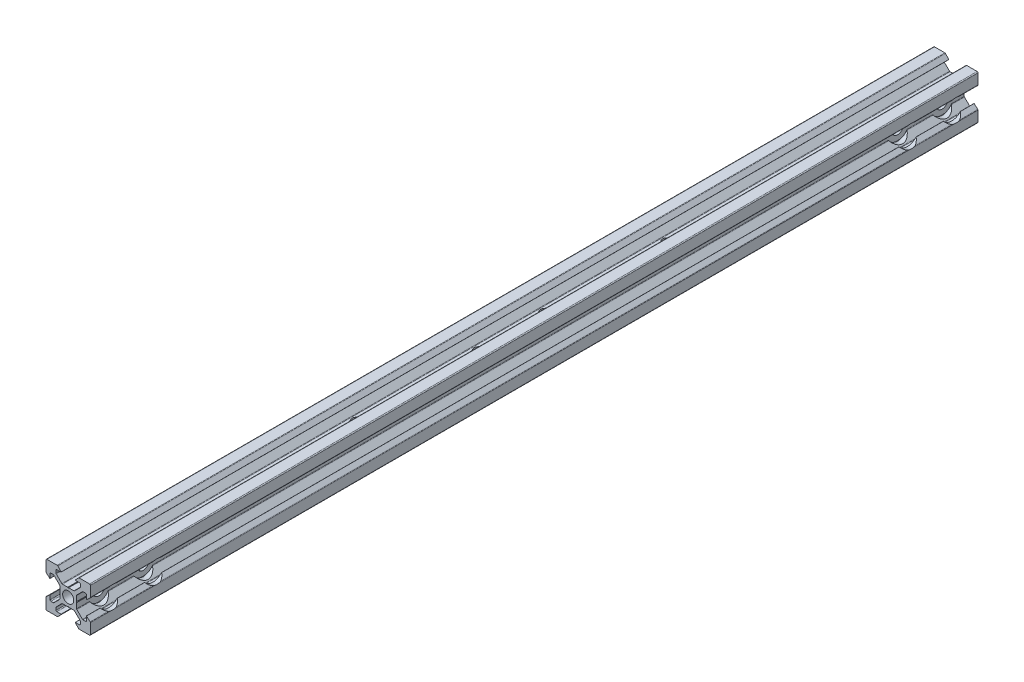
SolidWorks part; units mm, degrees
material "6063-T5"
ref_plane "前视基准面" through (0, 0, 0) normal (0, 0, 1) x (1, 0, 0)
ref_plane "上视基准面" through (0, 0, 0) normal (0, 1, 0) x (1, 0, 0)
ref_plane "右视基准面" through (0, 0, 0) normal (1, 0, 0) x (0, 0, -1)
sketch "草图1" plane through (0, 0, 0) normal (0, 0, 1) x (1, 0, 0)
  line L0 (0, 0) -> (13486.7145, 0) construction
  line L1 (0, 0) -> (0, 13486.7145) construction
  line L2 (0, 0) -> (9536.5473, 9536.5473) construction
  line L3 (0.2, 3.8) -> (2.5737, 3.8)
  line L4 (2.8565, 3.9172) -> (5.3828, 6.4435)
  line L5 (5.5, 6.7263) -> (5.5, 7.8)
  line L6 (5.1, 8.2) -> (3.2, 8.2)
  line L7 (3.1681, 8.2732) -> (4.6563, 9.8725)
  line L8 (4.9492, 10) -> (9.6, 10)
  line L9 (3.8, 0.2) -> (3.8, 2.5737)
  line L10 (3.9172, 2.8565) -> (6.4435, 5.3828)
  line L11 (6.7263, 5.5) -> (7.8, 5.5)
  line L12 (8.2, 5.1) -> (8.2, 3.2)
  line L13 (8.2732, 3.1681) -> (9.8725, 4.6563)
  line L14 (10, 4.9492) -> (10, 9.6)
  line L15 (3.8, -0.2) -> (3.8, -2.5737)
  line L16 (3.9172, -2.8565) -> (6.4435, -5.3828)
  line L17 (6.7263, -5.5) -> (7.8, -5.5)
  line L18 (8.2, -5.1) -> (8.2, -3.2)
  line L19 (8.2732, -3.1681) -> (9.8725, -4.6563)
  line L20 (10, -4.9492) -> (10, -9.6)
  line L21 (4.9492, -10) -> (9.6, -10)
  line L22 (3.1681, -8.2732) -> (4.6563, -9.8725)
  line L23 (5.1, -8.2) -> (3.2, -8.2)
  line L24 (5.5, -6.7263) -> (5.5, -7.8)
  line L25 (2.8565, -3.9172) -> (5.3828, -6.4435)
  line L26 (0.2, -3.8) -> (2.5737, -3.8)
  line L27 (-0.2, -3.8) -> (-2.5737, -3.8)
  line L28 (-2.8565, -3.9172) -> (-5.3828, -6.4435)
  line L29 (-5.5, -6.7263) -> (-5.5, -7.8)
  line L30 (-5.1, -8.2) -> (-3.2, -8.2)
  line L31 (-3.1681, -8.2732) -> (-4.6563, -9.8725)
  line L32 (-4.9492, -10) -> (-9.6, -10)
  line L33 (-10, -4.9492) -> (-10, -9.6)
  line L34 (-8.2732, -3.1681) -> (-9.8725, -4.6563)
  line L35 (-8.2, -5.1) -> (-8.2, -3.2)
  line L36 (-6.7263, -5.5) -> (-7.8, -5.5)
  line L37 (-3.9172, -2.8565) -> (-6.4435, -5.3828)
  line L38 (-3.8, -0.2) -> (-3.8, -2.5737)
  line L39 (-3.8, 0.2) -> (-3.8, 2.5737)
  line L40 (-3.9172, 2.8565) -> (-6.4435, 5.3828)
  line L41 (-6.7263, 5.5) -> (-7.8, 5.5)
  line L42 (-8.2, 5.1) -> (-8.2, 3.2)
  line L43 (-8.2732, 3.1681) -> (-9.8725, 4.6563)
  line L44 (-10, 4.9492) -> (-10, 9.6)
  line L45 (-4.9492, 10) -> (-9.6, 10)
  line L46 (-3.1681, 8.2732) -> (-4.6563, 9.8725)
  line L47 (-5.1, 8.2) -> (-3.2, 8.2)
  line L48 (-5.5, 6.7263) -> (-5.5, 7.8)
  line L49 (-2.8565, 3.9172) -> (-5.3828, 6.4435)
  line L50 (-0.2, 3.8) -> (-2.5737, 3.8)
  line L51 (-3.2, 8.2) -> (-3.1681, 8.2732)
  line L52 (3.2, 8.2) -> (3.1681, 8.2732)
  line L53 (-8.2, 3.2) -> (-8.2732, 3.1681)
  line L54 (8.2, 3.2) -> (8.2732, 3.1681)
  line L55 (8.2, -3.2) -> (8.2732, -3.1681)
  line L56 (3.2, -8.2) -> (3.1681, -8.2732)
  line L57 (-3.2, -8.2) -> (-3.1681, -8.2732)
  line L58 (-8.2, -3.2) -> (-8.2732, -3.1681)
  line L59 (-0.2, 3.8) -> (0, 3.6)
  line L60 (0, 3.6) -> (0.2, 3.8)
  line L61 (3.8, 0.2) -> (3.6, 0)
  line L62 (3.6, 0) -> (3.8, -0.2)
  line L63 (0.2, -3.8) -> (0, -3.6)
  line L64 (0, -3.6) -> (-0.2, -3.8)
  line L65 (-3.8, -0.2) -> (-3.6, 0)
  line L66 (-3.6, 0) -> (-3.8, 0.2)
  arc A0 (-4.9492, 10) -> (-4.6563, 9.8725) centre (-4.9492, 9.6) cw
  arc A1 (-5.1, 8.2) -> (-5.5, 7.8) centre (-5.1, 7.8) ccw
  arc A2 (-5.5, 6.7263) -> (-5.3828, 6.4435) centre (-5.1, 6.7263) ccw
  arc A3 (-2.8565, 3.9172) -> (-2.5737, 3.8) centre (-2.5737, 4.2) ccw
  arc A4 (-10, 9.6) -> (-9.6, 10) centre (-9.6, 9.6) cw
  arc A5 (-9.8725, 4.6563) -> (-10, 4.9492) centre (-9.6, 4.9492) cw
  arc A6 (-7.8, 5.5) -> (-8.2, 5.1) centre (-7.8, 5.1) ccw
  arc A7 (-6.4435, 5.3828) -> (-6.7263, 5.5) centre (-6.7263, 5.1) ccw
  arc A8 (-3.8, 2.5737) -> (-3.9172, 2.8565) centre (-4.2, 2.5737) ccw
  arc A9 (-10, -4.9492) -> (-9.8725, -4.6563) centre (-9.6, -4.9492) cw
  arc A10 (-8.2, -5.1) -> (-7.8, -5.5) centre (-7.8, -5.1) ccw
  arc A11 (-6.7263, -5.5) -> (-6.4435, -5.3828) centre (-6.7263, -5.1) ccw
  arc A12 (-3.9172, -2.8565) -> (-3.8, -2.5737) centre (-4.2, -2.5737) ccw
  arc A13 (-9.6, -10) -> (-10, -9.6) centre (-9.6, -9.6) cw
  arc A14 (-4.6563, -9.8725) -> (-4.9492, -10) centre (-4.9492, -9.6) cw
  arc A15 (-5.5, -7.8) -> (-5.1, -8.2) centre (-5.1, -7.8) ccw
  arc A16 (-5.3828, -6.4435) -> (-5.5, -6.7263) centre (-5.1, -6.7263) ccw
  arc A17 (-2.5737, -3.8) -> (-2.8565, -3.9172) centre (-2.5737, -4.2) ccw
  arc A18 (4.9492, -10) -> (4.6563, -9.8725) centre (4.9492, -9.6) cw
  arc A19 (5.1, -8.2) -> (5.5, -7.8) centre (5.1, -7.8) ccw
  arc A20 (5.5, -6.7263) -> (5.3828, -6.4435) centre (5.1, -6.7263) ccw
  arc A21 (2.8565, -3.9172) -> (2.5737, -3.8) centre (2.5737, -4.2) ccw
  arc A22 (10, -9.6) -> (9.6, -10) centre (9.6, -9.6) cw
  arc A23 (9.8725, -4.6563) -> (10, -4.9492) centre (9.6, -4.9492) cw
  arc A24 (7.8, -5.5) -> (8.2, -5.1) centre (7.8, -5.1) ccw
  arc A25 (6.4435, -5.3828) -> (6.7263, -5.5) centre (6.7263, -5.1) ccw
  arc A26 (3.8, -2.5737) -> (3.9172, -2.8565) centre (4.2, -2.5737) ccw
  arc A27 (9.8725, 4.6563) -> (10, 4.9492) centre (9.6, 4.9492) ccw
  arc A28 (7.8, 5.5) -> (8.2, 5.1) centre (7.8, 5.1) cw
  arc A29 (6.4435, 5.3828) -> (6.7263, 5.5) centre (6.7263, 5.1) cw
  arc A30 (3.8, 2.5737) -> (3.9172, 2.8565) centre (4.2, 2.5737) cw
  arc A31 (9.6, 10) -> (10, 9.6) centre (9.6, 9.6) cw
  arc A32 (4.6563, 9.8725) -> (4.9492, 10) centre (4.9492, 9.6) cw
  arc A33 (5.5, 7.8) -> (5.1, 8.2) centre (5.1, 7.8) ccw
  arc A34 (5.3828, 6.4435) -> (5.5, 6.7263) centre (5.1, 6.7263) ccw
  arc A35 (2.5737, 3.8) -> (2.8565, 3.9172) centre (2.5737, 4.2) ccw
  circle A36 centre (0, 0) radius 2
  point P12 (3.1, 8.2)
  point P18 (8.2, 3.1)
  point P28 (8.2, -3.1)
  point P34 (3.1, -8.2)
  point P41 (-3.1, -8.2)
  point P47 (-8.2, -3.1)
  point P54 (-8.2, 3.1)
  point P60 (-3.1, 8.2)
  point P62 (0, 0)
  point P112 (10, 4.775)
  point P115 (8.2, 5.5)
  point P118 (6.5607, 5.5)
  point P121 (3.8, 2.7393)
  point P124 (10, 10)
  point P127 (4.775, 10)
  point P130 (5.5, 8.2)
  point P133 (5.5, 6.5607)
  point P136 (2.7393, 3.8)
  point P168 (0, 0)
  dimension "D9" = 0.4
  dimension "D23" = 4
  dimension "D1" = 5.5
  dimension "D2" = 10
  dimension "D3" = 3.1
  dimension "D4" = 1.5
  dimension "D5" = 1.8
  dimension "D7" = 7.6
  dimension "D11" = 20
  dimension "D12" = 45
  dimension "D13" = 0.4
  dimension "D8" = 4
  dimension "D14" = 4
extrude "凸台-拉伸1" add sketch "草图1" along normal blind 400
hole_wizard "Ø5.2 (5.2) 直径孔1" positions "草图6" profile "草图7" hole size "Ø5.2" standard "GB" end condition through all
sketch "草图6" plane through (10, 0, 0) normal (1, 0, 0) x (0, 0, -1)
  line L0 (-400, 0) -> (0, 0) construction
  line L1 (-400, -9.6) -> (-400, -4.9492) construction
  line L2 (0, -9.6) -> (0, -4.9492) construction
  point P0 (-390, 0)
  point P2 (-370, 0)
  point P4 (-30, 0)
  point P6 (-10, 0)
  dimension "D1" = 20
  dimension "D2" = 10
  dimension "D3" = 20
  dimension "D4" = 10
sketch "草图7" plane through (10, 0, 390) normal (0, 1, 0) x (0, 0, -1)
  line L0 (0, 0) -> (0, 20)
  line L1 (0, 20) -> (2.6, 20)
  line L2 (2.6, 20) -> (2.6, 0)
  line L5 (2.6, 0) -> (0, 0)
  line L11 (0, -6.35) -> (0, 107.95) construction
  dimension "通孔孔直径" = 5.2
  dimension "通孔孔深度" = 20
hole_wizard "Ø10.0 (10) 直径孔1" positions "草图8" profile "草图9" hole size "Ø10.0" standard "GB"
sketch "草图8" plane through (10, 0, 0) normal (1, 0, 0) x (0, 0, -1)
  point P0 (-370, 0)
  point P3 (-390, 0)
  point P6 (-30, 0)
  point P9 (-10, 0)
sketch "草图9" plane through (10, 0, 370) normal (0, 1, 0) x (0, 0, -1)
  line L0 (0, 0) -> (0, 6.2)
  line L1 (0, 6.2) -> (5, 6.2)
  line L2 (5, 6.2) -> (5, 0)
  line L5 (5, 0) -> (0, 0)
  line L10 (0, 6.2) -> (-5, 6.2) construction
  line L11 (0, -6.35) -> (0, 107.95) construction
  dimension "孔直径" = 10
  dimension "孔深度" = 6.2
  dimension "导头角度" = 180
hole_wizard "M5 螺纹孔1" positions "草图5" profile "草图4" tap size "M5" standard "GB" end condition through all
sketch "草图5" plane through (0, 3.8, 0) normal (0, 1, 0) x (1, 0, 0)
  line L3 (0, -400) -> (0, 0) construction
  point P0 (0, -270)
  point P2 (0, -130)
  point P18 (0, -185)
  point P20 (0, -215)
  dimension "D1" = 130
  dimension "D2" = 140
  dimension "D3" = 30
  dimension "D4" = 55
sketch "草图4" plane through (0, 3.8, 270) normal (1, 0, 0) x (0, 0, 1)
  line L0 (0, 0) -> (0, 13.8)
  line L1 (0, 13.8) -> (2.1, 13.8)
  line L2 (2.1, 13.8) -> (2.1, 0)
  line L5 (2.1, 0) -> (0, 0)
  line L11 (0, -6.35) -> (0, 107.95) construction
  dimension "通孔螺纹孔钻头直径" = 4.2
  dimension "通孔螺纹孔钻头深度" = 13.8
cosmetic thread "孔螺蚊线2" parameters "D2"=5
cosmetic thread "孔螺蚊线3" parameters "D2"=5
cosmetic thread "孔螺蚊线4" parameters "D2"=5
cosmetic thread "孔螺蚊线5" parameters "D2"=5
hole_wizard "Ø5.0 (5) 直径孔1" positions "草图10" profile "草图11" hole size "Ø5.0" standard "GB"
sketch "草图10" plane through (0, 0, 400) normal (0, 0, 1) x (1, 0, 0)
  point P0 (0, 0)
sketch "草图11" plane through (0, 0, 400) normal (1, 0, 0) x (0, -1, 0)
  line L0 (0, 0) -> (0, 11.5022)
  line L1 (0, 11.5022) -> (2.5, 10)
  line L2 (2.5, 10) -> (2.5, 0)
  line L5 (2.5, 0) -> (0, 0)
  line L10 (0, 11.5022) -> (-2.5, 10) construction
  line L11 (0, -6.35) -> (0, 107.95) construction
  dimension "孔直径" = 5
  dimension "孔深度" = 10
  dimension "导头角度" = 118
hole_wizard "Ø5.0 (5) 直径孔2" positions "草图12" profile "草图13" hole size "Ø5.0" standard "GB"
sketch "草图12" plane through (0, 0, 0) normal (0, 0, -1) x (-1, 0, 0)
  point P0 (0, 0)
sketch "草图13" plane through (0, 0, 0) normal (1, 0, 0) x (0, 1, 0)
  line L0 (0, 0) -> (0, 11.5022)
  line L1 (0, 11.5022) -> (2.5, 10)
  line L2 (2.5, 10) -> (2.5, 0)
  line L5 (2.5, 0) -> (0, 0)
  line L10 (0, 11.5022) -> (-2.5, 10) construction
  line L11 (0, -6.35) -> (0, 107.95) construction
  dimension "孔直径" = 5
  dimension "孔深度" = 10
  dimension "导头角度" = 118
hole_wizard "M4 螺纹孔1" [suppressed] positions "草图14" profile "草图15" tap size "M4" standard "GB"
sketch "草图14" plane through (0, 3.8, 0) normal (0, 1, 0) x (1, 0, 0)
  line L0 (0, -127.9) -> (0, 0) construction
  line L1 (9.6, 0) -> (4.9492, 0) construction
  line L2 (9.6, -400) -> (4.9492, -400) construction
  line L3 (0, -400) -> (0, -272.1) construction
  point P0 (0, -380)
  point P2 (0, -20)
  dimension "D1" = 20
  dimension "D2" = 20
sketch "草图15" plane through (0, 3.8, 380) normal (1, 0, 0) x (0, 0, 1)
  line L0 (0, 0) -> (0, 13.8)
  line L1 (0, 13.8) -> (1.65, 13.8)
  line L2 (1.65, 13.8) -> (1.65, 0)
  line L5 (1.65, 0) -> (0, 0)
  line L11 (0, -6.35) -> (0, 107.95) construction
  dimension "通孔螺纹孔钻头直径" = 3.3
  dimension "通孔螺纹孔钻头深度" = 13.8
cosmetic thread "孔螺蚊线6" [suppressed] parameters "D2"=4
cosmetic thread "孔螺蚊线8" [suppressed] parameters "D2"=4
